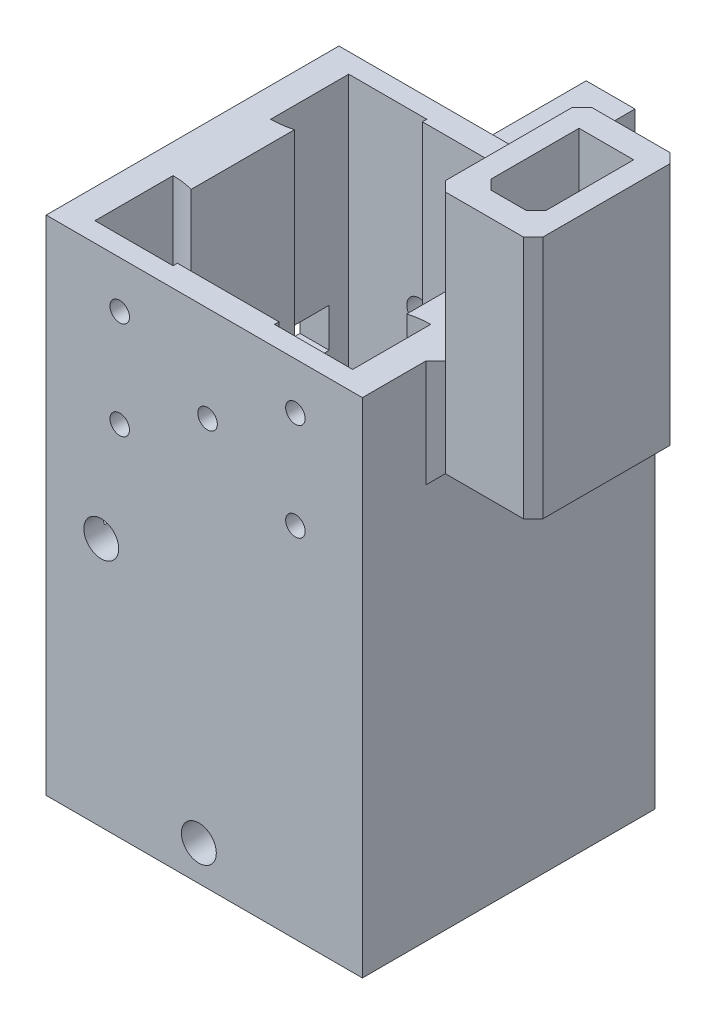
SolidWorks part; units mm, degrees
ref_plane "Front Plane" through (0, 0, 0) normal (0, 0, 1) x (1, 0, 0)
ref_plane "Top Plane" through (0, 0, 0) normal (0, 1, 0) x (1, 0, 0)
ref_plane "Right Plane" through (0, 0, 0) normal (1, 0, 0) x (0, 0, -1)
sketch "Sketch1" plane through (0, 0, 0) normal (0, 1, 0) x (1, 0, 0)
  line L0 (16.2, 0) -> (16.2, -30) construction
  line L1 (0, 0) -> (32.4, 0)
  line L2 (0, 0) -> (0, -30)
  line L3 (0, -30) -> (32.4, -30)
  line L4 (32.4, 0) -> (32.4, -30)
  line L5 (0, -15) -> (32.4, -15) construction
  circle A0 centre (6.2, -5) radius 1.75
  circle A1 centre (26.2, -5) radius 1.75
  circle A2 centre (26.2, -25) radius 1.75
  circle A3 centre (6.2, -25) radius 1.75
  dimension "D3" = 3.5
  dimension "D8" = 20
  dimension "D1" = 30
  dimension "D2" = 32.4
  dimension "D6" = 10
  dimension "D7" = 10
  dimension "D9" = 20
  dimension "D4" = 2
  dimension "D5" = 2
extrude "Boss-Extrude1" add sketch "Sketch1" along normal blind 25
sketch "Sketch2" plane through (0, 25, 0) normal (0, 1, 0) x (1, 0, 0)
  line L1 (16.2, 0) -> (16.2, -30) construction
  line L2 (32.4, 0) -> (0, 0) construction
  line L3 (0, -30) -> (32.4, -30) construction
  line L4 (0, -15) -> (32.4, -15) construction
  line L5 (0, 0) -> (0, -30) construction
  line L6 (32.4, -30) -> (32.4, 0) construction
  circle A0 centre (16.2, -15) radius 4
  dimension "D1" = 8
extrude "Cut-Extrude1" cut sketch "Sketch2" against normal blind 20
sketch "Sketch3" plane through (0, 25, 0) normal (0, 1, 0) x (1, 0, 0)
  line L0 (3, -10) -> (3, -20)
  line L1 (0, 0) -> (32.4, 0)
  line L2 (0, 0) -> (0, -30)
  line L3 (0, -30) -> (32.4, -30)
  line L4 (32.4, 0) -> (32.4, -30)
  line L5 (3, -2) -> (29.4, -2)
  line L6 (3, -2) -> (3, -28)
  line L7 (3, -28) -> (29.4, -28)
  line L8 (29.4, -2) -> (29.4, -28)
  line L9 (11, -28) -> (21.4, -28)
  line L10 (29.4, -20) -> (29.4, -10)
  line L11 (21.4, -2) -> (11, -2)
  arc A0 (11, -2) -> (3, -10) centre (3, -2) cw
  arc A1 (21.4, -28) -> (29.4, -20) centre (29.4, -28) cw
  arc A2 (29.4, -10) -> (21.4, -2) centre (29.4, -2) cw
  arc A3 (3, -20) -> (11, -28) centre (3, -28) cw
  circle M17 centre (16.2, -15) radius 4
  line M20 (0, 0) -> (0, -30)
  line M21 (0, -30) -> (32.4, -30)
  line M22 (32.4, -30) -> (32.4, 0)
  line M23 (32.4, 0) -> (0, 0)
  dimension "D5" = 8
  dimension "D6" = 8
  dimension "D7" = 8
  dimension "D8" = 8
  dimension "D1" = 3
  dimension "D2" = 3
  dimension "D3" = 2
  dimension "D4" = 2
extrude "Boss-Extrude2" add sketch "Sketch3" along normal blind 3 contours L5 L8 L7 L6 L0 M23 M20 M21 M22 | L0 A3 L7 A1 L8 A2 L5 A0 M17 | L2 L1 L4 L3
sketch "Sketch4" plane through (0, 28, 0) normal (0, 1, 0) x (1, 0, 0)
  line L0 (16.2, 0) -> (16.2, -30) construction
  line L9 (32.4, 0) -> (0, 0) construction
  line L10 (0, -30) -> (32.4, -30) construction
  line L11 (32.4, -15) -> (0, -15) construction
  line L12 (5.15, -20.2943) -> (5.15, -9.7057)
  line L13 (0, 0) -> (0, -30) construction
  line L14 (32.4, -30) -> (32.4, 0) construction
  line L15 (29.4, -20) -> (29.4, -28) construction
  line L16 (21.4, -28) -> (29.4, -28) construction
  line L17 (3, -28) -> (11, -28) construction
  line L18 (3, -20) -> (3, -28) construction
  line L19 (3, -2) -> (11, -2) construction
  line L20 (21.4, -2) -> (29.4, -2) construction
  line L21 (29.4, -2) -> (29.4, -10) construction
  line L22 (3, -2) -> (3, -10) construction
  line L23 (0, -30) -> (32.4, -30)
  line L24 (0, 0) -> (0, -30)
  line L25 (32.4, 0) -> (0, 0)
  line L26 (32.4, -30) -> (32.4, 0)
  line L27 (29.4, -20) -> (29.4, -28)
  line L28 (21.4, -28) -> (29.4, -28)
  line L29 (3, -28) -> (11, -28)
  line L30 (3, -20) -> (3, -28)
  line L31 (3, -2) -> (11, -2)
  line L32 (21.4, -2) -> (29.4, -2)
  line L33 (29.4, -2) -> (29.4, -10)
  line L34 (3, -2) -> (3, -10)
  line L35 (10.9873, -2.45) -> (21.4127, -2.45)
  line L36 (27.25, -9.7057) -> (27.25, -20.2943)
  line L37 (10.9873, -27.55) -> (21.4127, -27.55)
  arc A0 (29.4, -20) -> (21.4, -28) centre (29.4, -28) ccw construction
  arc A1 (11, -28) -> (3, -20) centre (3, -28) ccw construction
  arc A2 (21.4, -2) -> (29.4, -10) centre (29.4, -2) ccw construction
  arc A3 (3, -10) -> (11, -2) centre (3, -2) ccw construction
  arc A4 (29.4, -20) -> (27.25, -20.2943) centre (29.4, -28) ccw
  arc A5 (11, -28) -> (10.9873, -27.55) centre (3, -28) ccw
  arc A6 (21.4, -2) -> (21.4127, -2.45) centre (29.4, -2) ccw
  arc A7 (3, -10) -> (5.15, -9.7057) centre (3, -2) ccw
  arc A8 (10.9873, -2.45) -> (11, -2) centre (3, -2) ccw
  arc A9 (5.15, -20.2943) -> (3, -20) centre (3, -28) ccw
  arc A10 (21.4127, -27.55) -> (21.4, -28) centre (29.4, -28) ccw
  arc A11 (27.25, -9.7057) -> (29.4, -10) centre (29.4, -2) ccw
  point P15 (16.2, -15)
  dimension "D1" = 22.1
  dimension "D2" = 11.05
  dimension "D3" = 25.1
  dimension "D4" = 12.55
extrude "Boss-Extrude3" add sketch "Sketch4" along normal blind 23.5
sketch "Sketch5" plane through (0, 0, 0) normal (0, 0, -1) x (-1, 0, 0)
  line L0 (-32.4, 28) -> (0, 28) construction
  line L1 (-32.4, 28) -> (0, 28)
  line L2 (-5.15, 28) -> (-5.15, 36.9803) construction
  line L3 (0, 51.5) -> (0, 0) construction
  line L4 (-27.25, 28) -> (-27.25, 39.4314) construction
  line L5 (-32.4, 51.5) -> (-32.4, 0) construction
  line L6 (-16.2, 28) -> (-16.2, 36.5707) construction
  circle A0 centre (-22.2, 49) radius 1.25
  circle A1 centre (-10.2, 34) radius 1.25
  dimension "D6" = 2.5
  dimension "D7" = 2.5
  dimension "D1" = 6
  dimension "D2" = 12
  dimension "D3" = 5.15
  dimension "D4" = 5.15
  dimension "D5" = 6
  dimension "D8" = 15
extrude "Cut-Extrude2" cut sketch "Sketch5" along direction (0, 0, 1) on the side against the normal up to surface (2.45 mm away) contours A0 | A1
sketch "Sketch6" plane through (0, 0, 0) normal (-1, 0, 0) x (0, 0, 1)
  line L0 (0, 28) -> (30, 28) construction
  line L1 (0, 28) -> (30, 28)
  line L2 (0, 51.5) -> (0, 0) construction
  line L3 (4, 28) -> (26, 28)
  line L4 (4, 28) -> (4, 32)
  line L5 (4, 32) -> (26, 32)
  line L6 (26, 28) -> (26, 32)
  line L7 (30, 51.5) -> (30, 0) construction
  dimension "D1" = 4
  dimension "D2" = 4
  dimension "D3" = 4
extrude "Cut-Extrude3" cut sketch "Sketch6" along direction (1, 0, 0) on the side against the normal up to surface (5.15 mm away) contours L1 L6 L5 L4
sketch "Sketch7" plane through (32.4, 0, 0) normal (1, 0, 0) x (0, 0, -1)
  line L1 (-7.5, 51.5) -> (-22.5, 51.5)
  line L2 (-7.5, 51.5) -> (-7.5, 41.5)
  line L3 (-7.5, 41.5) -> (-22.5, 41.5)
  line L4 (-22.5, 51.5) -> (-22.5, 41.5)
  line L11 (-30, 51.5) -> (0, 51.5) construction
  point P5 (-15, 51.5)
  point P7 (-15, 51.5)
  dimension "D1" = 15
  dimension "D2" = 10
extrude "Boss-Extrude4" add sketch "Sketch7" along normal blind 10
sketch "Sketch8" plane through (0, 51.5, 0) normal (0, 1, 0) x (1, 0, 0)
  line L0 (32.4, 0) -> (32.4, -30) construction
  line L1 (34.6, -10) -> (40.2, -10)
  line L2 (34.6, -10) -> (34.6, -20)
  line L3 (34.6, -20) -> (40.2, -20)
  line L4 (40.2, -10) -> (40.2, -20)
  line L6 (42.4, -7.5) -> (32.4, -7.5) construction
  point P6 (32.4, -15)
  point P7 (34.6, -15)
  point P10 (37.4, -7.5)
  point P13 (37.4, -10)
  dimension "D1" = 5.6
  dimension "D2" = 10
extrude "Cut-Extrude4" cut sketch "Sketch8" against normal blind 15
chamfer "Chamfer1" distance 1 angle 45 2 edges at (40.2, 46.5, 20) (34.6, 46.5, 20)
sketch "Sketch11" plane through (0, 0, 30) normal (0, 0, 1) x (1, 0, 0)
  line L1 (0, 0) -> (32.4, 0) construction
  line L2 (7.5358, 46.7) -> (25.5358, 46.7) construction
  line L3 (7.5358, 46.7) -> (7.5358, 36.7) construction
  circle A0 centre (7.5358, 46.7) radius 1
  circle A1 centre (25.5358, 46.7) radius 1
  circle A2 centre (7.5358, 36.7) radius 1
  circle A3 centre (25.5358, 36.7) radius 1
  circle A4 centre (16.5358, 41.7) radius 1
  point P6 (16.5358, 46.7)
  point P13 (7.5358, 41.7)
  dimension "D1" = 2
  dimension "D2" = 2
  dimension "D3" = 2
  dimension "D4" = 2
  dimension "D5" = 41.7
  dimension "D6" = 18
  dimension "D8" = 2
  dimension "D7" = 10
extrude "Cut-Extrude5" cut sketch "Sketch11" against normal blind 5
chamfer "Chamfer3" distance 1 angle 45 5 edges at (42.4, 46.5, 22.5) (42.4, 46.5, 7.5) (32.4, 46.5, 7.5) (32.4, 46.5, 22.5) (32.4, 41.5, 15)
sketch "Sketch12" plane through (0, 0, 30) normal (0, 0, 1) x (1, 0, 0)
  line L0 (32.4, 51.5) -> (32.4, 0) construction
  line L1 (0, 51.5) -> (32.4, 51.5)
  line L2 (0, 51.5) -> (0, 31.5)
  line L3 (0, 31.5) -> (32.4, 31.5)
  line L4 (32.4, 51.5) -> (32.4, 31.5)
  dimension "D1" = 20
extrude "Boss-Extrude5" [suppressed] add sketch "Sketch12" along normal blind 12
sketch "Sketch13" [suppressed] plane through (0, 0, 42) normal (0, 0, 1) x (1, 0, 0)
  line L0 (32.4, 51.5) -> (0, 51.5) construction
  line L1 (0, 51.5) -> (0, 31.5) construction
  line L2 (7.2, 46.5) -> (25.2, 46.5) construction
  line L3 (7.2, 46.5) -> (7.2, 36.5) construction
  circle A0 centre (7.2, 46.5) radius 1
  circle A1 centre (25.2, 46.5) radius 1
  circle A2 centre (7.2, 36.5) radius 1
  circle A3 centre (25.2, 36.5) radius 1
  circle A4 centre (16.2, 41.5) radius 1
  point P6 (16.2, 46.5)
  point P13 (7.2, 41.5)
  point P25 (16.2, 51.5)
  point P29 (0, 41.5)
  dimension "D1" = 2
  dimension "D2" = 2
  dimension "D3" = 2
  dimension "D4" = 2
  dimension "D6" = 18
  dimension "D8" = 2
  dimension "D7" = 10
extrude "Cut-Extrude6" [suppressed] cut sketch "Sketch13" against normal up to next
chamfer "Chamfer4" [suppressed] distance 1 angle 45
sketch "Sketch15" plane through (0, 51.5, 0) normal (0, 1, 0) x (1, 0, 0)
  line L1 (32.4, -7.5) -> (41.4, -7.5)
  line L2 (42.4, -8.5) -> (41.4, -7.5) construction
  line L3 (41.4, -7.5) -> (33.4, -7.5) construction
  line L4 (41.4, -7.5) -> (42.4, -8.5)
  line L5 (42.4, -8.5) -> (42.4, -21.5)
  line L6 (42.4, -21.5) -> (41.4, -22.5)
  line L7 (41.4, -22.5) -> (32.4, -22.5)
  line L10 (34.6, -10) -> (34.6, -19)
  line L11 (35.6, -20) -> (34.6, -19) construction
  line L12 (34.6, -10) -> (34.6, -19) construction
  line L13 (34.6, -19) -> (35.6, -20)
  line L14 (35.6, -20) -> (39.2, -20)
  line L15 (39.2, -20) -> (40.2, -19)
  line L16 (40.2, -19) -> (40.2, -10)
  line L17 (40.2, -10) -> (34.6, -10) construction
  line L18 (40.2, -19) -> (40.2, -10) construction
  line L19 (40.2, -10) -> (34.6, -10)
  line L20 (32.4, -7.5) -> (32.4, -22.5)
  line L21 (32.4, 0) -> (32.4, -30) construction
extrude "Boss-Extrude6" add sketch "Sketch15" along normal blind 15
chamfer "Chamfer5" distance 1 angle 45 2 edges at (32.4, 59, 7.5) (32.4, 59, 22.5)
hole_wizard "3/32 (0.140625) Dowel Hole1" positions "Sketch17" profile "Sketch18" hole size "3/32" standard "ANSI Inch"
sketch "Sketch17" plane through (0, 0, 30) normal (0, 0, 1) x (1, 0, 0)
  line L0 (5.6459, 25.5998) -> (15.6459, 25.5998) construction
  line L1 (15.6459, 25.5998) -> (15.6459, 3.5998) construction
  point P0 (5.6459, 25.5998)
  point P2 (15.6459, 3.5998)
  dimension "D1" = 10
  dimension "D2" = 22
sketch "Sketch18" plane through (5.6459, 25.5998, 30) normal (1, 0, 0) x (0, -1, 0)
  line L0 (0, 0) -> (0, 13.7731)
  line L1 (0, 13.7731) -> (1.7859, 12.7)
  line L2 (1.7859, 12.7) -> (1.7859, 0)
  line L5 (1.7859, 0) -> (0, 0)
  line L10 (0, 13.7731) -> (-1.7859, 12.7) construction
  line L11 (0, -6.35) -> (0, 107.95) construction
  dimension "Hole Dia." = 3.5719
  dimension "Hole Depth" = 12.7
  dimension "Drill Angle" = 118
sketch "Sketch19" plane through (0, 0, 0) normal (0, 0, -1) x (-1, 0, 0)
  line L0 (0, 51.5) -> (0, 32.5777) construction
  line L1 (0, 51.5) -> (0, 0) construction
  line L2 (0, 32.5777) -> (-2.8312, 32.5777) construction
  line L4 (-0.3312, 29.0777) -> (-5.3312, 29.0777)
  line L5 (-0.3312, 29.0777) -> (-0.3312, 36.0777)
  line L6 (-0.3312, 36.0777) -> (-5.3312, 36.0777)
  line L7 (-5.3312, 29.0777) -> (-5.3312, 36.0777)
  line L8 (-0.3312, 29.0777) -> (-5.3312, 36.0777) construction
  line L9 (-0.3312, 36.0777) -> (-5.3312, 29.0777) construction
  dimension "D1" = 18.9223
  dimension "D2" = 7
  dimension "D3" = 5
  dimension "D4" = 0.6625
extrude "Boss-Extrude7" add sketch "Sketch19" along normal blind 25
